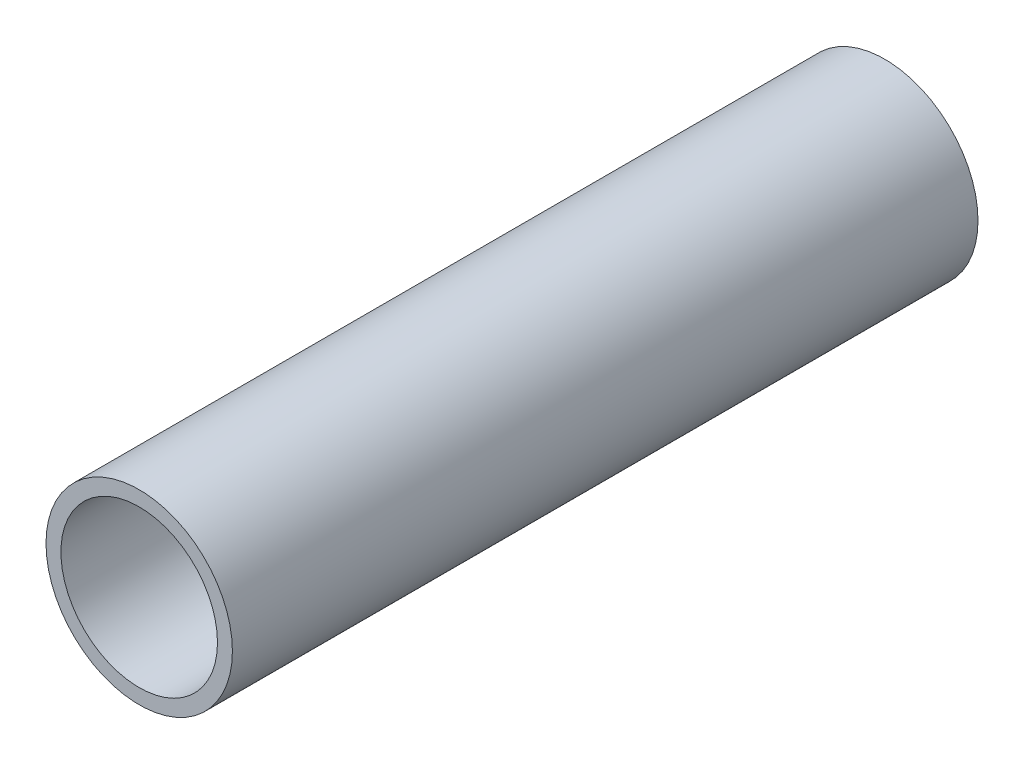
SolidWorks part; units mm, degrees
ref_plane "Alzado" through (0, 0, 0) normal (0, 0, 1) x (1, 0, 0)
ref_plane "Planta" through (0, 0, 0) normal (0, 1, 0) x (1, 0, 0)
ref_plane "Vista lateral" through (0, 0, 0) normal (1, 0, 0) x (0, 0, -1)
sketch "Croquis1" plane through (0, 0, 0) normal (0, 0, 1) x (1, 0, 0)
  circle A0 centre (0, 0) radius 6.25
  circle A1 centre (0, 0) radius 5.25
  dimension "D1" = 12.5
  dimension "D2" = 1
extrude "Saliente-Extruir1" add sketch "Croquis1" along normal mid plane 50
